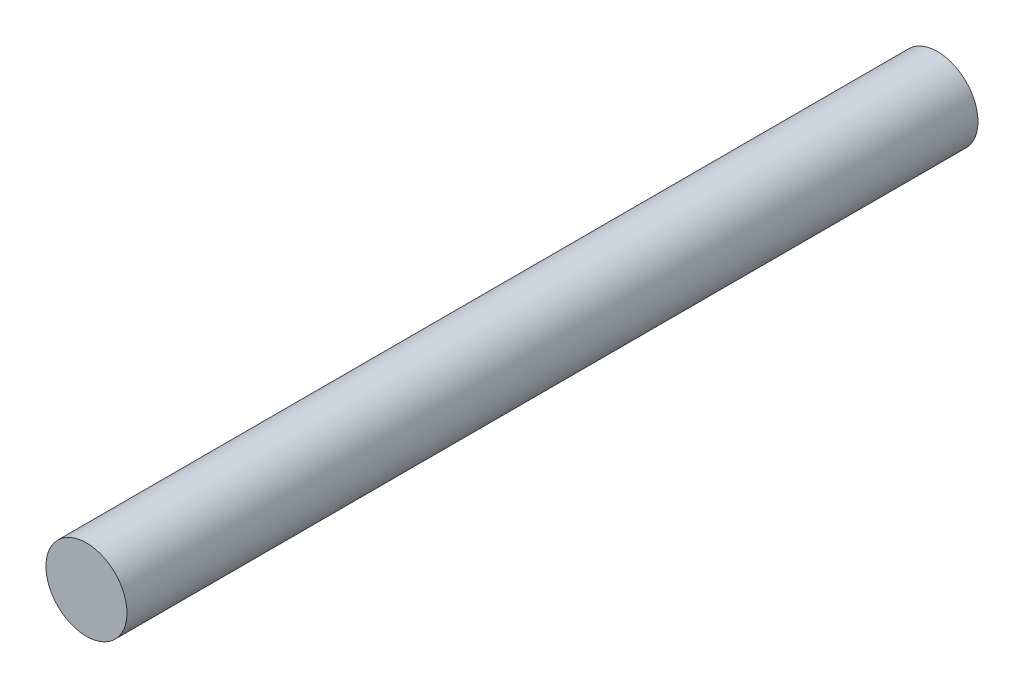
SolidWorks part; units mm, degrees
ref_plane "Plan de face" through (0, 0, 0) normal (0, 0, 1) x (1, 0, 0)
ref_plane "Plan de dessus" through (0, 0, 0) normal (0, 1, 0) x (1, 0, 0)
ref_plane "Plan de droite" through (0, 0, 0) normal (1, 0, 0) x (0, 0, -1)
sketch "Esquisse1" plane through (0, 0, 0) normal (0, 1, 0) x (1, 0, 0)
  line L0 (1, 0) -> (0, 0)
  line L1 (0, 0) -> (0, -21)
  line L2 (0, -21) -> (1, -21)
  line L3 (1, -21) -> (1, 0)
  line L4 (0, 0) -> (0, -21) construction
revolve "Révolution1" add sketch "Esquisse1" angle 360 about L4
